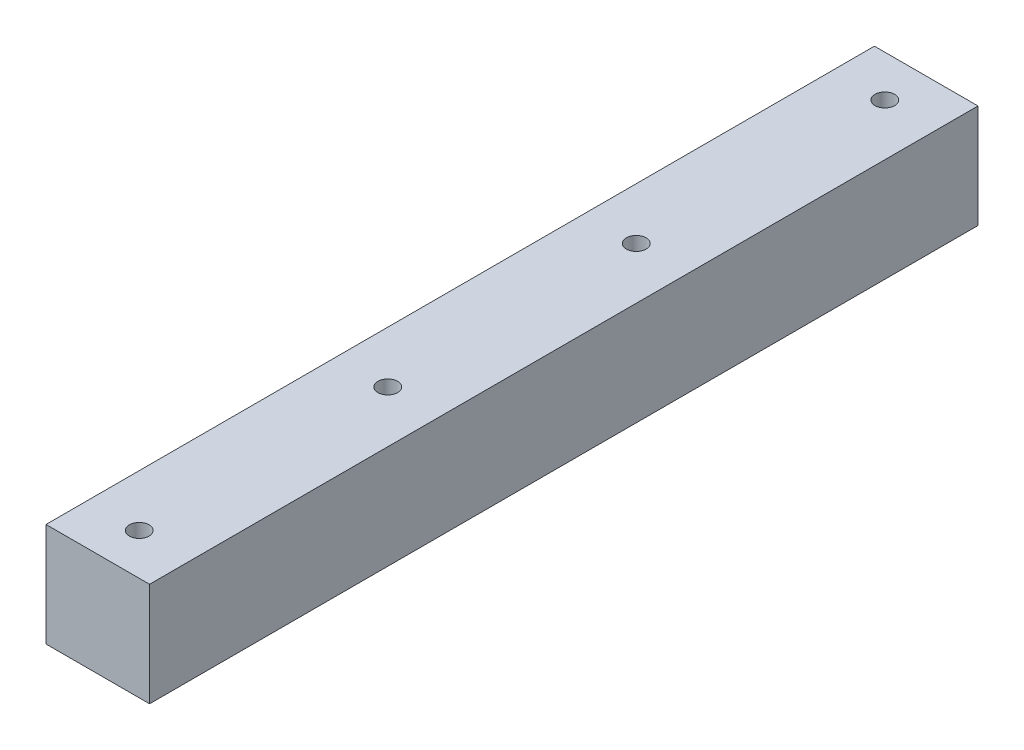
SolidWorks part; units mm, degrees
ref_plane "Ebene vorne" through (0, 0, 0) normal (0, 0, 1) x (1, 0, 0)
ref_plane "Ebene oben" through (0, 0, 0) normal (0, 1, 0) x (1, 0, 0)
ref_plane "Ebene rechts" through (0, 0, 0) normal (1, 0, 0) x (0, 0, -1)
sketch "Skizze1" plane through (0, 0, 0) normal (0, 1, 0) x (1, 0, 0)
  line L1 (-25, -200) -> (25, -200)
  line L2 (-25, -200) -> (-25, 200)
  line L3 (-25, 200) -> (25, 200)
  line L4 (25, -200) -> (25, 200)
  line L5 (-25, -200) -> (25, 200) construction
  line L6 (-25, 200) -> (25, -200) construction
  point P0 (0, 0)
  dimension "D1" = 50
  dimension "D2" = 400
extrude "Aufsatz-Linear austragen1" add sketch "Skizze1" along normal blind 50
hole_wizard "Ø9.5 (9.5) Durchmesser Bohrung1" positions "Skizze3" profile "Skizze2" hole size "Ø9.5" standard "DIN"
sketch "Skizze3" plane through (0, 50, 0) normal (0, 1, 0) x (1, 0, 0)
  line L0 (0, -27.5) -> (0, 27.5) construction
  line L1 (-25, -200) -> (25, -200) construction
  point P0 (0, -180)
  dimension "D1" = 20
sketch "Skizze2" plane through (0, 50, 180) normal (1, 0, 0) x (0, 0, 1)
  line L0 (0, 0) -> (0, 22.8541)
  line L1 (0, 22.8541) -> (4.75, 20)
  line L2 (4.75, 20) -> (4.75, 0)
  line L5 (4.75, 0) -> (0, 0)
  line L10 (0, 22.8541) -> (-4.75, 20) construction
  line L11 (0, -6.35) -> (0, 107.95) construction
  dimension "Bohrerdurchmesser" = 9.5
  dimension "Bohrungstiefe" = 20
  dimension "Spitzenwinkel" = 118
pattern_linear "Lineares Muster1" count 4 spacing 120 along (0, 0, -1) of "Ø9.5 (9.5) Durchmesser Bohrung1"
equation "\"D1@Skizze3\" = round ( \"D2@Skizze1\" - int ( ( \"D2@Skizze1\" - 40 ) / 120 ) * 120 ) / 2"
equation "\"D1@Lineares Muster1\"  = ( \"D2@Skizze1\" - 2 * \"D1@Skizze3\" ) / 120 + 1"
